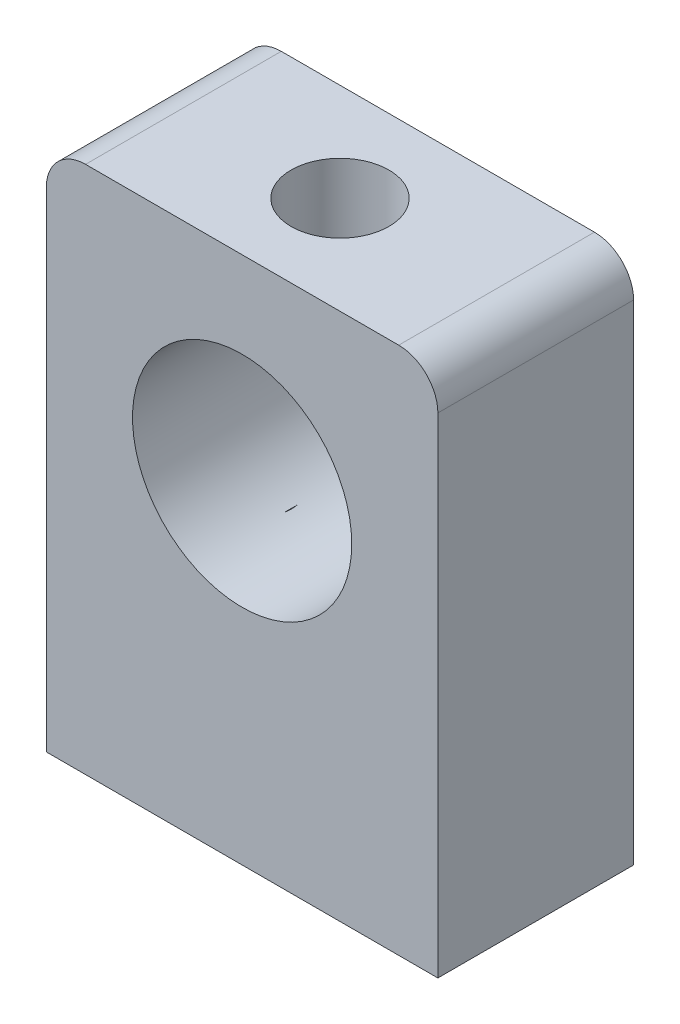
SolidWorks part; units mm, degrees
ref_plane "前视基准面" through (0, 0, 0) normal (0, 0, 1) x (1, 0, 0)
ref_plane "上视基准面" through (0, 0, 0) normal (0, 1, 0) x (1, 0, 0)
ref_plane "右视基准面" through (0, 0, 0) normal (1, 0, 0) x (0, 0, -1)
other "Configuration Table"
sketch "草图1" plane through (0, 0, 0) normal (0, 0, 1) x (1, 0, 0)
  line L1 (-9.0616, 9.7774) -> (6.9384, 9.7774)
  line L2 (-11.0616, 7.7774) -> (-11.0616, -17.2226)
  line L3 (-11.0616, -17.2226) -> (8.9384, -17.2226)
  line L4 (8.9384, 7.7774) -> (8.9384, -17.2226)
  arc A0 (6.9384, 9.7774) -> (8.9384, 7.7774) centre (6.9384, 7.7774) cw
  arc A1 (-9.0616, 9.7774) -> (-11.0616, 7.7774) centre (-9.0616, 7.7774) ccw
  circle A2 centre (-1.0616, -0.2226) radius 5.6
  point P6 (8.9384, 9.7774)
  point P9 (-11.0616, 9.7774)
  dimension "D3" = 2
  dimension "D4" = 11.2
  dimension "D6" = 10
  dimension "D1" = 20
  dimension "D2" = 27
  dimension "D5" = 10
extrude "凸台-拉伸1" add sketch "草图1" along normal blind 10
sketch "草图9" plane through (0, 9.7774, 0) normal (0, 1, 0) x (1, 0, 0)
  line L0 (6.9384, 0) -> (-9.0616, 0) construction
  line L1 (8.9384, -10) -> (8.9384, 0) construction
  circle A1 centre (-1.0616, -5) radius 2.5
  dimension "D1" = 5
  dimension "D2" = 5
  dimension "D3" = 10
extrude "切除-拉伸1" cut sketch "草图9" against normal blind 6
sketch "草图11" plane through (0, -17.2226, 0) normal (0, -1, 0) x (1, 0, 0)
  line L0 (-11.0616, 10) -> (8.9384, 10) construction
  line L1 (-11.0616, 0) -> (8.9384, 0) construction
  line L3 (-11.0616, 10) -> (-11.0616, 0) construction
  line L4 (8.9384, 10) -> (8.9384, 0) construction
  circle A0 centre (-6.0616, 5) radius 2.5
  circle A1 centre (3.9384, 5) radius 2.5
  dimension "D1" = 5
  dimension "D2" = 5
  dimension "D3" = 5
  dimension "D4" = 5
  dimension "D5" = 5
  dimension "D6" = 5
extrude "切除-拉伸2" cut sketch "草图11" against normal blind 12
